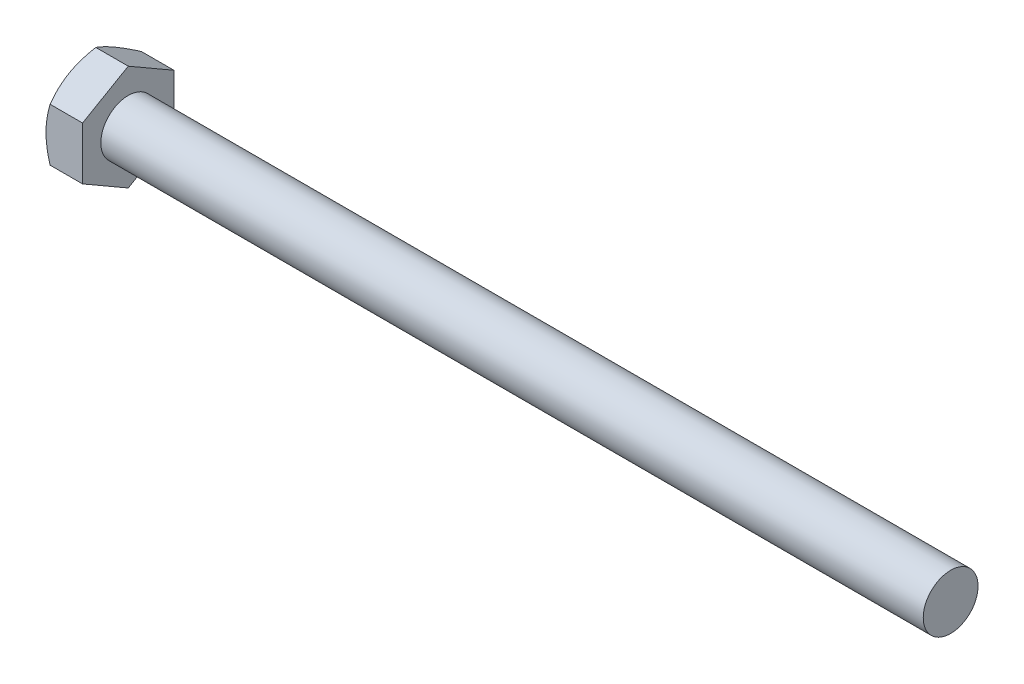
SolidWorks part; units mm, degrees
extrude "BaseHead" add sketch "Sketch1" along normal blind 4
sketch "Sketch1" plane through (0, 0, 0) normal (1, 0, 0) x (0, 0, -1)
  line L0 (5, 2.8868) -> (5, -2.8868)
  line L1 (-5, 2.8868) -> (-5, -2.8868)
  line L2 (5, -2.8868) -> (0, -5.7735)
  line L3 (0, -5.7735) -> (-5, -2.8868)
  line L4 (5, 2.8868) -> (0, 5.7735)
  line L5 (0, 5.7735) -> (-5, 2.8868)
  dimension "Width_flats" = 10
  dimension "D2" = 120
  dimension "D3" = 5
  dimension "D4" = 5
  dimension "D5" = 5
ref_plane "Plane1" through (0, 0, 0) normal (0, 0, 1) x (1, 0, 0)
ref_plane "Plane2" through (0, 0, 0) normal (0, 1, 0) x (1, 0, 0)
ref_plane "Plane3" through (0, 0, 0) normal (1, 0, 0) x (0, 0, -1)
sketch "BodySke" plane through (0, 0, 0) normal (0, 0, 1) x (1, 0, 0)
  line L0 (0, 2.8868) -> (0, -2.8868) construction
  line L1 (0, 0) -> (94, 0)
  line L2 (0, 0) -> (0, 3)
  line L3 (0, 3) -> (94, 3)
  line L4 (94, 0) -> (94, 3)
  line L5 (4, 5.7735) -> (4, 2.8868) construction
  line L7 (0, 0) -> (96.52, 0) construction
  line L10 (5, 15.24) -> (5, -1.27) construction
  line L11 (76, 15.24) -> (76, -1.27) construction
  line L12 (4, 2.8868) -> (4, -2.8868) construction
  dimension "Diameter" = 6
revolve "BaseBody" add sketch "BodySke" angle 360 about L7
cosmetic thread "ThreadCosmetic"
sketch "Sketch3" plane through (0, 0, 0) normal (0, 0, 1) x (1, 0, 0)
  line L0 (0, 5) -> (3.3333, 10.7735)
  line L1 (0, 5.7735) -> (0, 2.8868) construction
  line L2 (3.3333, 10.7735) -> (3.3333, 15.7735)
  line L3 (3.3333, 15.7735) -> (-10, 15.7735)
  line L4 (-10, 15.7735) -> (-10, 5)
  line L5 (-10, 5) -> (0, 5)
  line L6 (0, 0) -> (99.06, 0) construction
  line L7 (4, 5.7735) -> (0, 5.7735) construction
  dimension "D4" = 5
  dimension "D1" = 5
  dimension "D2" = 5
  dimension "D3" = 10
  dimension "Head_ch_ang" = 30
revolve "HeadChamfer" cut sketch "Sketch3" angle 360 about L6
sketch "SkeExt" plane through (0, 0, 0) normal (0, 0, 1) x (1, 0, 0)
  line L0 (4, 2.8868) -> (4, -2.8868) construction
  circle A0 centre (90, 0) radius 0.8
  dimension "D2" = 1.6
  dimension "D1" = 86
extrude "Cut-Extrude1" [suppressed] cut sketch "SkeExt" against normal through all and the other way through all
sketch "Sketch2" plane through (9.6236, 0.011, 5) normal (0, 0, 1) x (1, 0, 0)
  line L1 (-5.6236, -2.8978) -> (-5.6236, -5.7845) construction
  line L4 (-9.6236, -0.011) -> (86.8964, -0.011) construction
  circle A0 centre (-7.6236, -0.011) radius 1
  dimension "D1" = 2
  dimension "d2" = 2
extrude "Cut-Extrude2" [suppressed] cut sketch "Sketch2" against normal through all
pattern_circular "CirPattern1" [suppressed] count 2 every 60 about axis through (0, 0, 0) along (1, 0, 0)
sketch "Sketch5" plane through (0, -5.0498, -0.0755) normal (-1, 0, 0) x (0, 0, 1)
  circle A0 centre (0.0755, 5.0498) radius 4
  arc A2 (-2.4245, 9.3799) -> (-4.9245, 5.0498) centre (0.0755, 5.0498) ccw construction
  dimension "D1" = 8
extrude "Cut-Extrude3" [suppressed] cut sketch "Sketch5" against normal blind 0.8
equation "\"D3@Sketch1\" = \"Width_flats@Sketch1\" / 2"
equation "\"D4@Sketch1\" = \"D3@Sketch1\""
equation "\"D5@Sketch1\" = \"D4@Sketch1\""
equation "\"D1@Sketch3\" = \"Width_flats@Sketch1\" / 2"
equation "\"Thread_length@ThreadCosmetic\" = ((sgn( (\"Length@BodySke\" - \"Advance@BodySke\" ) - \"Thread_nom@BodySke\" )-1)*( (\"Length@BodySke\" - \"Advance@BodySke\" ) - \"Thread_nom@BodySke\" ))/-2+ \"Thread_nom@BodySke\""
